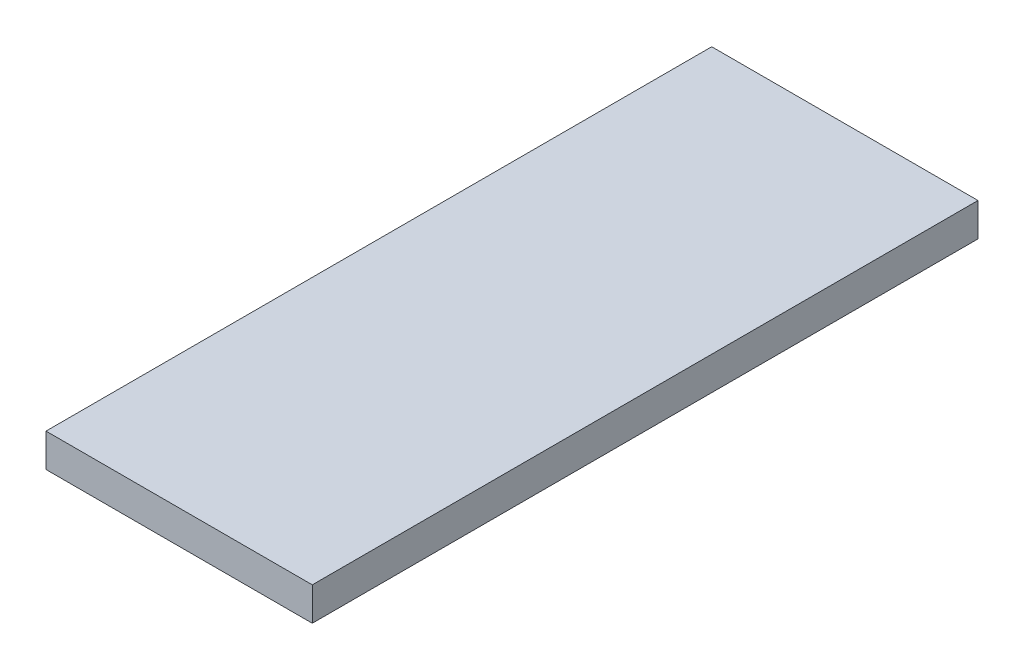
SolidWorks part; units mm, degrees
ref_plane "Спереди" through (0, 0, 0) normal (0, 0, 1) x (1, 0, 0)
ref_plane "Сверху" through (0, 0, 0) normal (0, 1, 0) x (1, 0, 0)
ref_plane "Справа" through (0, 0, 0) normal (1, 0, 0) x (0, 0, -1)
sketch "Эскиз1" plane through (0, 0, 0) normal (0, 1, 0) x (1, 0, 0)
  line L1 (0, 0) -> (40, 0)
  line L2 (0, 0) -> (0, 100)
  line L3 (0, 100) -> (40, 100)
  line L4 (40, 0) -> (40, 100)
extrude "Бобышка-Вытянуть1" add sketch "Эскиз1" along normal blind 5
